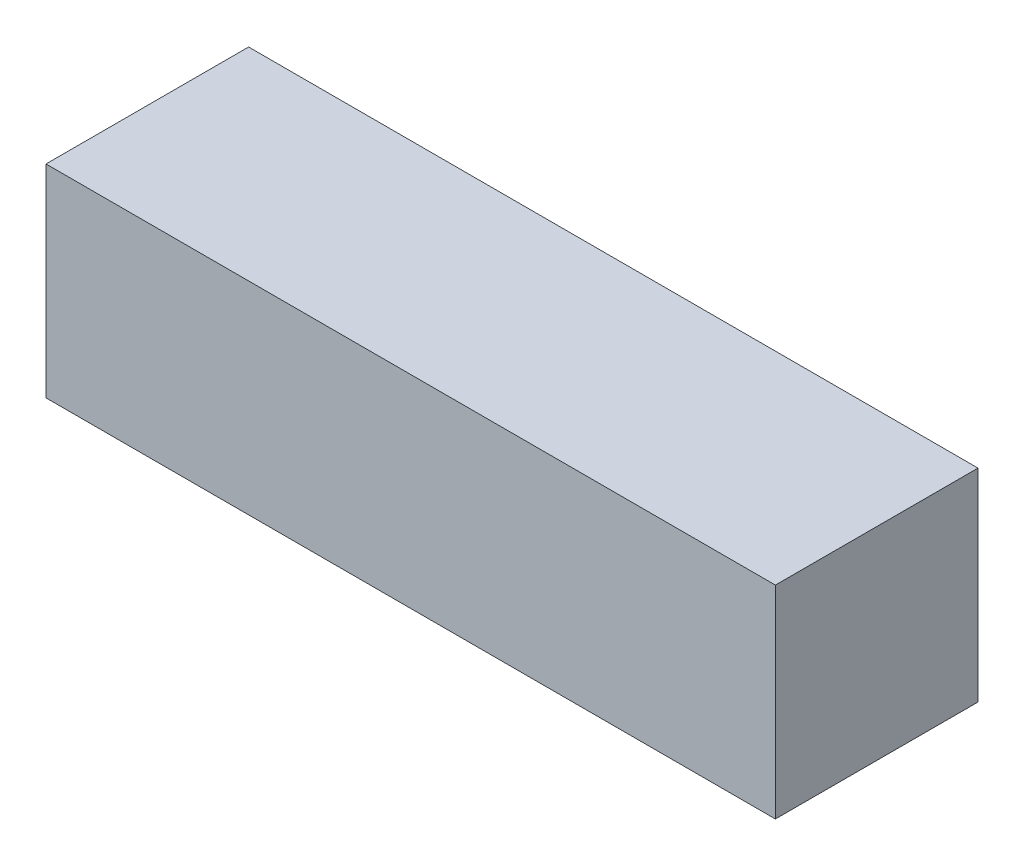
SolidWorks part; units mm, degrees
ref_plane "前基準面" through (0, 0, 0) normal (0, 0, 1) x (1, 0, 0)
ref_plane "上基準面" through (0, 0, 0) normal (0, 1, 0) x (1, 0, 0)
ref_plane "右基準面" through (0, 0, 0) normal (1, 0, 0) x (0, 0, -1)
sketch "草圖1" plane through (0, 0, 0) normal (0, 0, 1) x (1, 0, 0)
  line L1 (-24.0943, 8.2137) -> (11.9057, 8.2137)
  line L2 (-24.0943, 8.2137) -> (-24.0943, -1.7863)
  line L3 (-24.0943, -1.7863) -> (11.9057, -1.7863)
  line L4 (11.9057, 8.2137) -> (11.9057, -1.7863)
  dimension "D1" = 36
  dimension "D2" = 10
extrude "填料-伸長1" add sketch "草圖1" along normal blind 10
